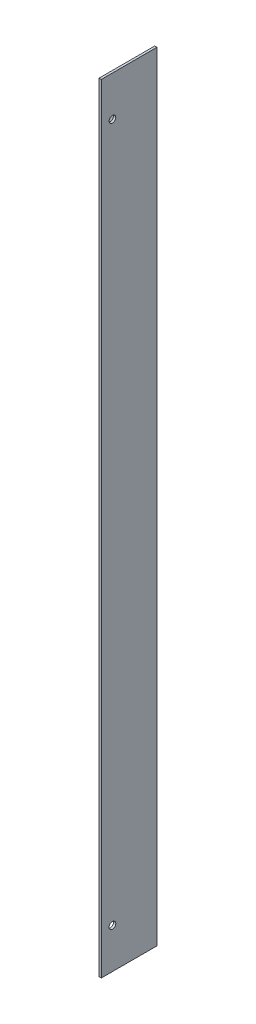
SolidWorks part; units mm, degrees
material "Plástico personalizado"
ref_plane "Alzado" through (0, 0, 0) normal (0, 0, 1) x (1, 0, 0)
ref_plane "Planta" through (0, 0, 0) normal (0, 1, 0) x (1, 0, 0)
ref_plane "Vista lateral" through (0, 0, 0) normal (1, 0, 0) x (0, 0, -1)
sketch "Croquis1" plane through (0, 0, 0) normal (0, 0, 1) x (1, 0, 0)
  line L0 (-55.4418, 61.1804) -> (-79.4418, 37.1804)
  line L1 (-79.4418, -264.8196) -> (-79.4418, 37.1804)
  line L4 (-55.4418, 61.1804) -> (-55.4418, -288.8196)
  line L5 (-55.4418, -288.8196) -> (-79.4418, -264.8196)
  circle A0 centre (-74.4418, 21.1804) radius 1.5
  circle A1 centre (-74.4418, -248.8196) radius 1.5
  circle A2 centre (-74.4418, -58.8196) radius 1.5
  dimension "D1" = 5
  dimension "D4" = 24
  dimension "D9" = 5
  dimension "D2" = 350
  dimension "D3" = 5
  dimension "D5" = 40
  dimension "D6" = 40
  dimension "D7" = 45
  dimension "D8" = 45
  dimension "D10" = 120
sketch "Croquis2" plane through (0, 0, 0) normal (0, 0, 1) x (1, 0, 0)
  line L1 (-55.4418, 61.1804) -> (-54.4418, 61.1804)
  line L2 (-55.4418, 61.1804) -> (-55.4418, -288.8196)
  line L3 (-55.4418, -288.8196) -> (-54.4418, -288.8196)
  line L4 (-54.4418, 61.1804) -> (-54.4418, -288.8196)
  dimension "D1" = 1
  dimension "D2" = 350
extrude "Saliente-Extruir2" add sketch "Croquis2" along normal blind 25
sketch "Croquis5" plane through (-54.4418, 0, 0) normal (1, 0, 0) x (0, 0, -1)
  line L0 (-25, 61.1804) -> (0, 61.1804) construction
  line L1 (-25, -288.8196) -> (0, -288.8196) construction
  line L2 (-25, -288.8196) -> (-25, 61.1804) construction
  circle A0 centre (-20, 43.1804) radius 1.5
  circle A1 centre (-20, -270.8196) radius 1.5
  dimension "D1" = 18
  dimension "D4" = 5
  dimension "D2" = 18
  dimension "D3" = 5
extrude "Cortar-Extruir2" cut sketch "Croquis5" against normal blind 1
extrude "Saliente-Extruir3" add sketch "Croquis1" along normal blind 1
